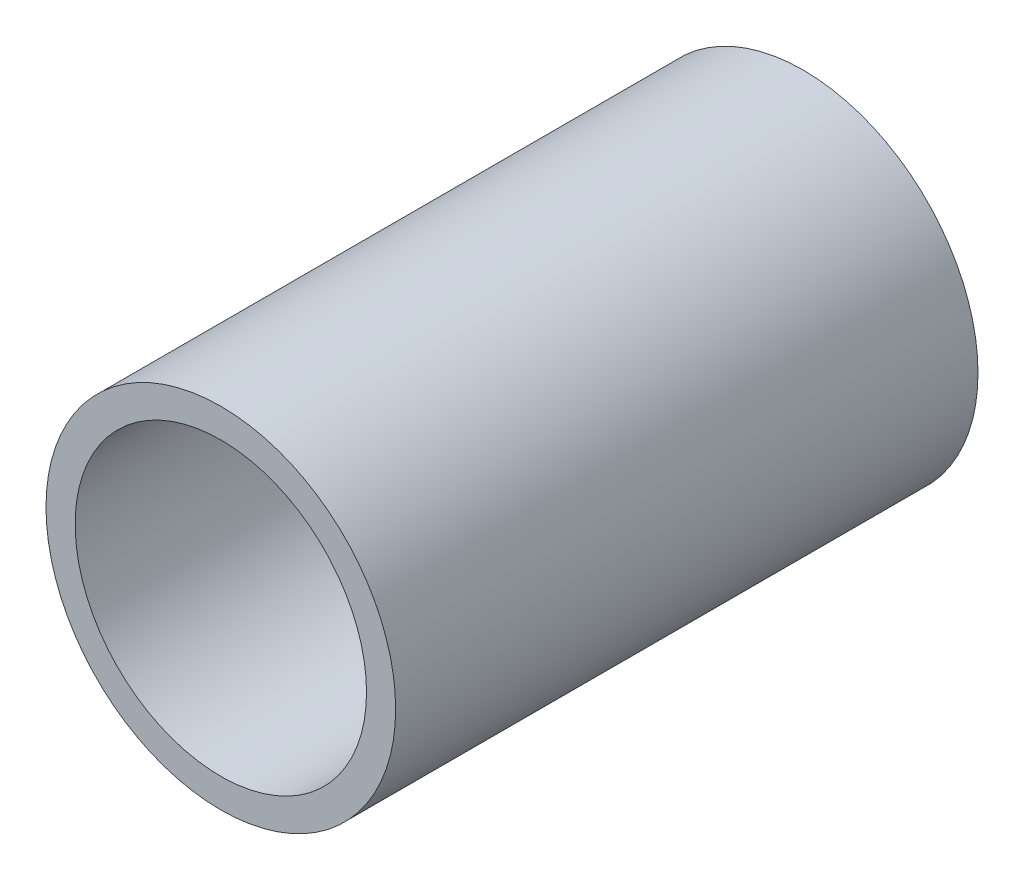
SolidWorks part; units mm, degrees
ref_plane "Front Plane" through (0, 0, 0) normal (0, 0, 1) x (1, 0, 0)
ref_plane "Top Plane" through (0, 0, 0) normal (0, 1, 0) x (1, 0, 0)
ref_plane "Right Plane" through (0, 0, 0) normal (1, 0, 0) x (0, 0, -1)
sketch "Sketch1" plane through (0, 0, 0) normal (0, 0, 1) x (1, 0, 0)
  circle A0 centre (0, 0) radius 19.0627
  circle A1 centre (0, 0) radius 15.8877
  dimension "D1" = 38.1254
  dimension "ID" = 31.7754
extrude "Extrude1" add sketch "Sketch1" along normal mid plane 63.5
sketch "Sketch2" plane through (0, 0, 0) normal (1, 0, 0) x (0, 0, -1)
  line L0 (-31.75, -15.8877) -> (31.75, -15.8877) construction
  line L3 (31.75, 15.8877) -> (-31.75, 15.8877) construction
  line L5 (-31.75, -15.8877) -> (31.75, -15.8877)
  line L6 (31.75, 15.8877) -> (-31.75, 15.8877)
sketch "Sketch4" plane through (0, 0, 31.75) normal (0, 0, 1) x (1, 0, 0)
  line L0 (0, 0) -> (-11.2343, 11.2343)
  line L1 (0, -8.7592) -> (0, 8.7592) construction
  circle A0 centre (0, 0) radius 15.8877 construction
  dimension "D1" = 45
